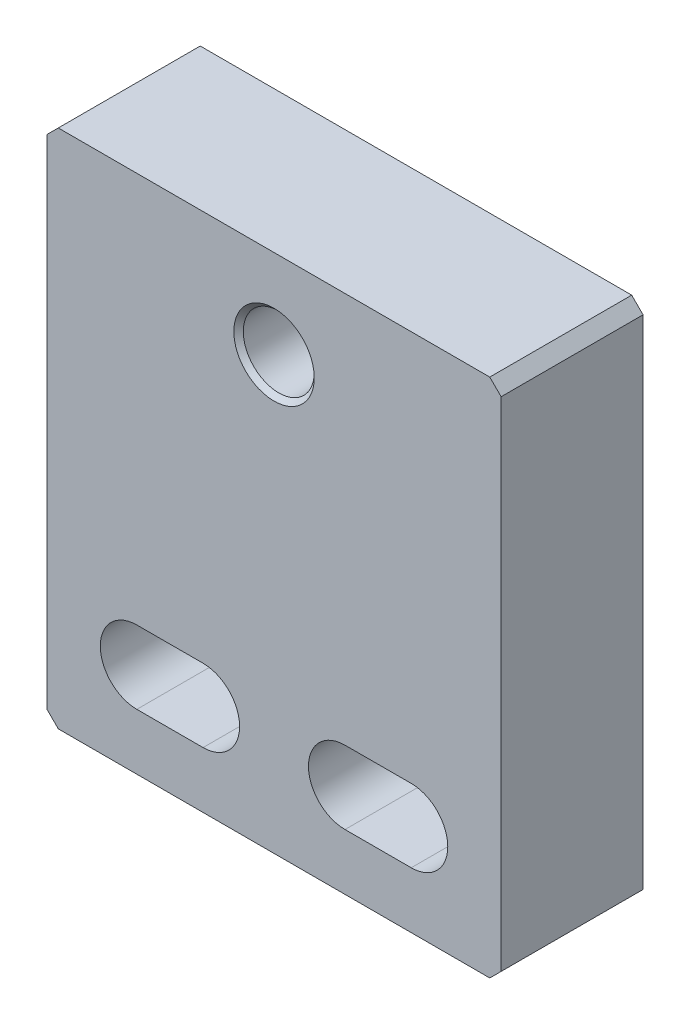
SolidWorks part; units mm, degrees
material "6061-T6 Al"
ref_plane "Front Plane" through (0, 0, 0) normal (0, 0, 1) x (1, 0, 0)
ref_plane "Top Plane" through (0, 0, 0) normal (0, 1, 0) x (1, 0, 0)
ref_plane "Right Plane" through (0, 0, 0) normal (1, 0, 0) x (0, 0, -1)
sketch "Sketch6" plane through (0, 0, 0) normal (0, 0, 1) x (1, 0, 0)
  line L2 (-28.956, 57.404) -> (28.956, 57.404)
  line L3 (-30.48, 55.88) -> (-30.48, -10.922)
  line L4 (-28.956, -12.446) -> (28.956, -12.446)
  line L5 (30.48, 55.88) -> (30.48, -10.922)
  line L6 (0, 57.404) -> (0, 0) construction
  line L7 (9.525, 0) -> (18.415, 0) construction
  line L13 (-30.48, 55.88) -> (-28.956, 57.404)
  line L14 (28.956, 57.404) -> (30.48, 55.88)
  line L15 (28.956, -12.446) -> (30.48, -10.922)
  line L16 (-30.48, -10.922) -> (-28.956, -12.446)
  line L18 (9.525, 4.9022) -> (18.415, 4.9022)
  line L19 (9.525, -4.9022) -> (18.415, -4.9022)
  line L20 (-9.525, 0) -> (-18.415, 0) construction
  line L21 (-9.525, 4.9022) -> (-18.415, 4.9022)
  line L22 (-9.525, -4.9022) -> (-18.415, -4.9022)
  arc A7 (9.525, 4.9022) -> (9.525, -4.9022) centre (9.525, 0) ccw
  arc A8 (18.415, -4.9022) -> (18.415, 4.9022) centre (18.415, 0) ccw
  arc A9 (-9.525, 4.9022) -> (-9.525, -4.9022) centre (-9.525, 0) cw
  arc A10 (-18.415, -4.9022) -> (-18.415, 4.9022) centre (-18.415, 0) cw
  point P7 (13.97, 0)
  point P15 (-13.97, 0)
  dimension "D1" = 69.85
  dimension "D2" = 27.94
  dimension "D3" = 60.96
  dimension "D4" = 12.446
  dimension "D5" = 8.89
  dimension "D7" = 1.524
extrude "Boss-Extrude1" add sketch "Sketch6" against normal blind 19.05
hole_wizard "3/8-16 Tapped Hole1" positions "Sketch10" profile "Sketch11" tap size "3/8-16" standard "ANSI Inch" end condition through all
sketch "Sketch10" plane through (0, 0, 0) normal (0, 0, 1) x (1, 0, 0)
  line L0 (10.4775, 0) -> (-10.4775, 0) construction
  point P0 (0, 45.5295)
  dimension "D1" = 45.5295
sketch "Sketch11" plane through (0, 45.5295, 0) normal (1, 0, 0) x (0, -1, 0)
  line L0 (0, 0) -> (0, 19.05)
  line L1 (0, 19.05) -> (4.7625, 19.05)
  line L2 (4.7625, 19.05) -> (4.7625, 0.635)
  line L3 (4.7625, 0.635) -> (5.3975, 0)
  line L5 (5.3975, 0) -> (0, 0)
  line L6 (-4.7625, 0.635) -> (-5.3975, 0) construction
  line L11 (0, -6.35) -> (0, 107.95) construction
  dimension "Thread Major Dia." = 9.525
  dimension "Thru Tap Drill Depth" = 19.05
  dimension "Near C'Sink Dia." = 10.795
  dimension "Near C'Sink Angle" = 90
